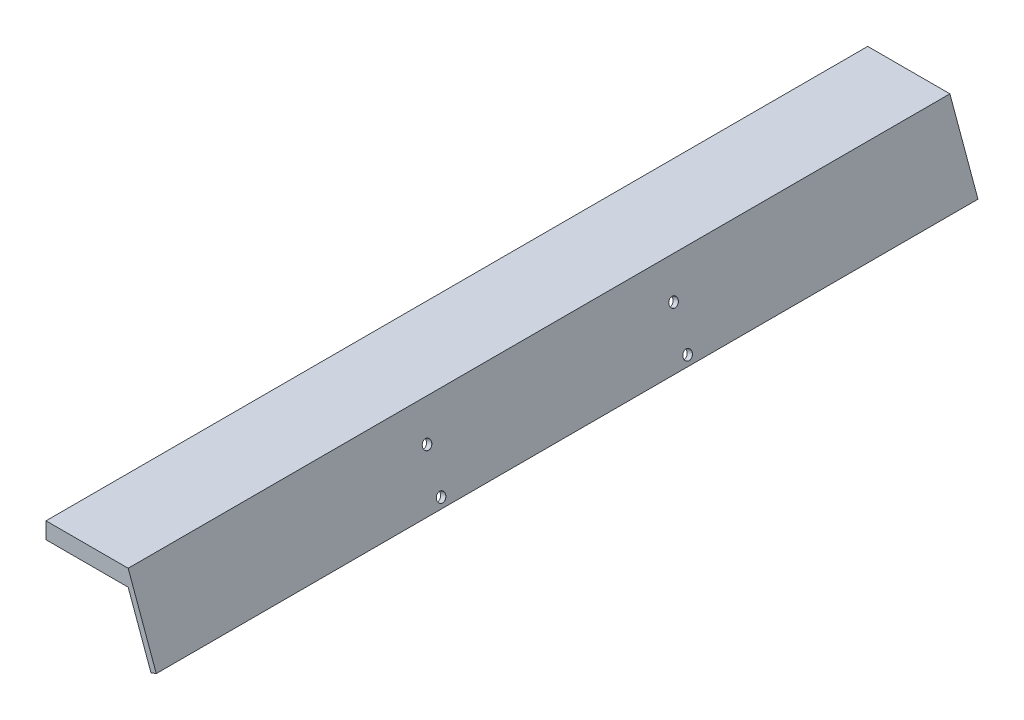
SolidWorks part; units mm, degrees
ref_plane "Front Plane" through (0, 0, 0) normal (0, 0, 1) x (1, 0, 0)
ref_plane "Top Plane" through (0, 0, 0) normal (0, 1, 0) x (1, 0, 0)
ref_plane "Right Plane" through (0, 0, 0) normal (1, 0, 0) x (0, 0, -1)
sketch "Sketch4" plane through (0, 0, 0) normal (0, 0, 1) x (1, 0, 0)
  line L0 (0, 0) -> (50, 0)
  line L1 (50, 0) -> (67.101, -46.9846)
  line L2 (67.101, -46.9846) -> (63.8871, -48.1544)
  line L3 (63.8871, -48.1544) -> (50, -10)
  line L4 (50, -10) -> (0, -10)
  line L5 (0, -10) -> (0, 0)
  dimension "D1" = 50
  dimension "D2" = 10
  dimension "D3" = 50
  dimension "D4" = 20
extrude "Boss-Extrude6" add sketch "Sketch4" along normal blind 500
sketch "Sketch5" plane through (0, 0, 0) normal (0, 1, 0) x (1, 0, 0)
  line L0 (50, -500) -> (50, 0) construction
  line L1 (35, -340) -> (15, -340) construction
  line L2 (35, -340) -> (35, -160) construction
  line L3 (35, -160) -> (15, -160) construction
  line L4 (15, -340) -> (15, -160) construction
  line L5 (35, -340) -> (15, -160) construction
  line L6 (35, -160) -> (15, -340) construction
  point P0 (25, -250)
  point P7 (50, -250)
  dimension "D1" = 180
  dimension "D2" = 20
  dimension "D3" = 15
sketch "Sketch6" plane through (44.1511, 16.0697, 0) normal (0.9397, 0.342, 0) x (0, 0, -1)
  line L0 (-500, -26.4979) -> (0, -26.4979) construction
  line L5 (-500, -26.4979) -> (0, -26.4979) construction
sketch "Sketch7" plane through (0, 0, 0) normal (0, 1, 0) x (1, 0, 0)
  line L0 (50, 0) -> (0, 0) construction
  line L1 (50, -500) -> (0, -500) construction
  point P0 (25, -15)
  point P2 (25, -25)
  point P4 (25, -485)
  point P6 (25, -475)
  dimension "D1" = 10
  dimension "D2" = 15
  dimension "D3" = 15
  dimension "D4" = 10
hole_wizard "M4 Clearance Hole1" positions "Sketch7" profile "Sketch8" hole size "M4" standard "ISO"
sketch "Sketch8" plane through (25, 0, 15) normal (1, 0, 0) x (0, 0, 1)
  line L0 (0, 0) -> (0, 48.1544)
  line L1 (0, 48.1544) -> (2.25, 48.1544)
  line L2 (2.25, 48.1544) -> (2.25, 0.025)
  line L3 (2.25, 0.025) -> (2.275, 0)
  line L5 (2.275, 0) -> (0, 0)
  line L6 (-2.25, 0.025) -> (-2.275, 0) construction
  line L11 (0, -6.35) -> (0, 107.95) construction
  dimension "Thru Hole Dia." = 4.5
  dimension "Thru Hole Depth" = 48.1544
  dimension "Near C'Sink Dia." = 4.55
  dimension "Near C'Sink Angle" = 90
sketch "Sketch9" plane through (44.1511, 16.0697, 0) normal (0.9397, 0.342, 0) x (0, 0, -1)
  line L1 (-325, -37.1419) -> (-175, -37.1419) construction
  line L2 (-175, -37.1419) -> (-175, -62.1419) construction
  line L3 (-175, -62.1419) -> (-325, -62.1419) construction
  line L4 (-325, -62.1419) -> (-325, -37.1419) construction
  line L5 (-325, -37.1419) -> (-175, -62.1419) construction
  line L7 (-325, -62.1419) -> (-175, -37.1419) construction
  line L9 (0, -67.101) -> (0, -17.101) construction
  point P0 (-325, -37.1419)
  point P2 (-325, -62.1419)
  point P4 (-175, -62.1419)
  point P6 (-175, -37.1419)
  dimension "D1" = 25
  dimension "D2" = 150
  dimension "D3" = 175
hole_wizard "M5 Clearance Hole1" positions "Sketch9" profile "Sketch10" hole size "M5" standard "ISO" end condition through all
sketch "Sketch10" plane through (56.8544, -18.8323, 325) normal (0, 0, 1) x (-0.342, 0.9397, 0)
  line L0 (0, 0) -> (0, 63.4544)
  line L1 (0, 63.4544) -> (2.75, 63.4544)
  line L2 (2.75, 63.4544) -> (2.75, 0.025)
  line L3 (2.75, 0.025) -> (2.775, 0)
  line L5 (2.775, 0) -> (0, 0)
  line L6 (-2.75, 0.025) -> (-2.775, 0) construction
  line L11 (0, -6.35) -> (0, 107.95) construction
  dimension "Thru Hole Dia." = 5.5
  dimension "Thru Hole Depth" = 63.4544
  dimension "Near C'Sink Dia." = 5.55
  dimension "Near C'Sink Angle" = 90
